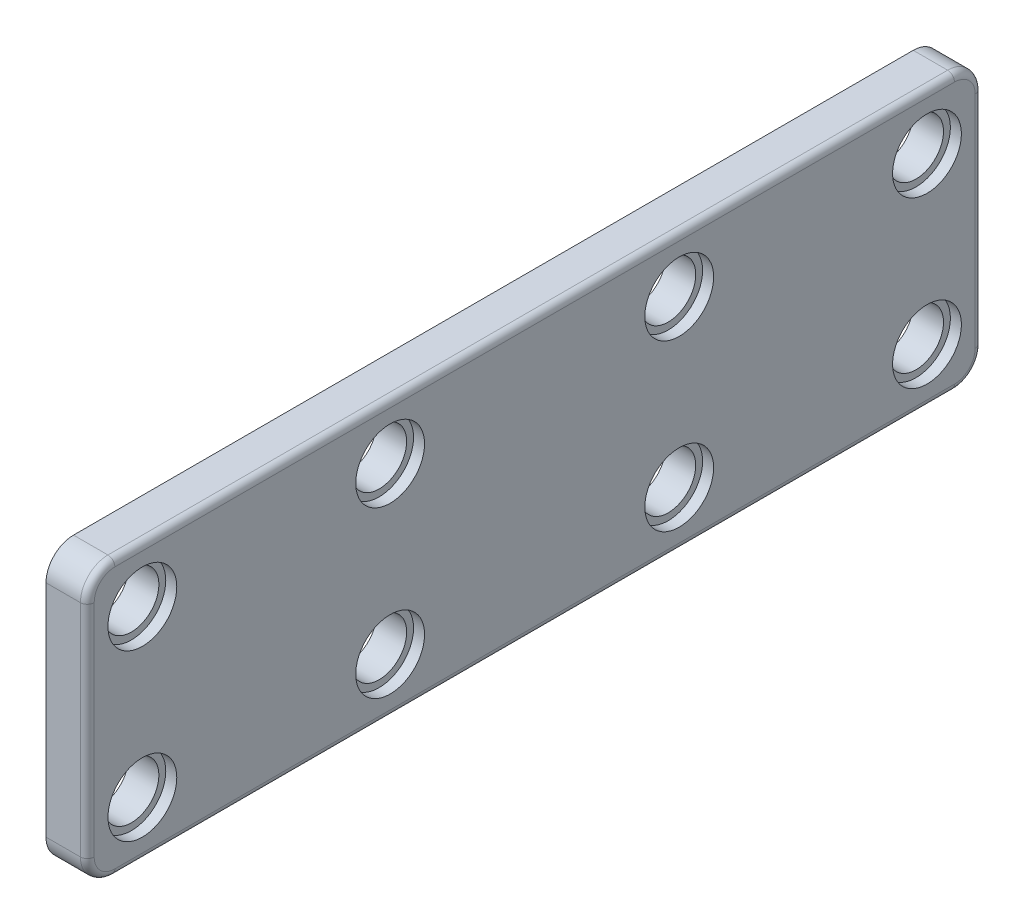
SolidWorks part; units mm, degrees
ref_plane "Front Plane" through (0, 0, 0) normal (0, 0, 1) x (1, 0, 0)
ref_plane "Top Plane" through (0, 0, 0) normal (0, 1, 0) x (1, 0, 0)
ref_plane "Right Plane" through (0, 0, 0) normal (1, 0, 0) x (0, 0, -1)
sketch "Sketch2" plane through (0, 0, 0) normal (0, 0, 1) x (1, 0, 0)
  line L1 (-1.5, -10) -> (1.5, -10)
  line L2 (-1.5, -10) -> (-1.5, 10)
  line L3 (-1.5, 10) -> (1.5, 10)
  line L4 (1.5, -10) -> (1.5, 10)
  line L5 (-1.5, -10) -> (1.5, 10) construction
  line L6 (-1.5, 10) -> (1.5, -10) construction
  point P0 (0, 0)
  dimension "D1" = 20
  dimension "D2" = 3
extrude "Boss-Extrude2" add sketch "Sketch2" along normal blind 65
fillet "Fillet3" radius 2 1 edges at (0, 10, 65)
fillet "Fillet4" radius 2 1 edges at (0, -10, 65)
fillet "Fillet5" radius 2 1 edges at (0, 10, 0)
fillet "Fillet6" radius 2 1 edges at (0, -10, 0)
sketch "Sketch3" plane through (1.5, 0, 0) normal (1, 0, 0) x (0, 0, -1)
  line L0 (-86.0874, 0) -> (15.1847, 0) construction
  line L2 (-65, -8) -> (-65, 8) construction
  line L3 (-32.5, 10) -> (-32.5, -20.1361) construction
  line L4 (-63, 10) -> (-2, 10) construction
  point P3 (-61, 6)
  dimension "D1" = 6
  dimension "D2" = 4
hole_wizard "CBORE for M5 Hex Head Bolt1" positions "Sketch5" profile "Sketch4" counterbore size "M5" standard "DIN"
sketch "Sketch5" plane through (1.5, 0, 0) normal (1, 0, 0) x (0, 0, -1)
  point P0 (-61, 6)
sketch "Sketch4" plane through (1.5, 6, 61) normal (0, 1, 0) x (0, 0, -1)
  line L0 (0, 0) -> (0, 5.1781)
  line L1 (0, 5.1781) -> (2, 4)
  line L2 (2, 4) -> (2, 0.8)
  line L3 (2, 0.8) -> (2.5, 0.8)
  line L4 (2.5, 0.8) -> (2.5, 0)
  line L5 (2.5, 0) -> (0, 0)
  line L10 (0, 5.1781) -> (-2, 4) construction
  line L11 (0, -6.35) -> (0, 107.95) construction
  dimension "Hole Dia." = 4
  dimension "Hole Depth" = 4
  dimension "C'Bore Dia." = 5
  dimension "C'Bore Depth" = 0.8
  dimension "Drill Angle" = 119
pattern_linear "LPattern1" count 2 spacing 18 along (0, 0, -1) count 2 spacing 12 along (0, -1, 0) of "CBORE for M5 Hex Head Bolt1"
ref_plane "Plane1" through (0, 0, 32.5) normal (0, 0, 1) x (0, -1, 0)
mirror "Mirror16" about plane through (0, 0, 32.5) normal (0, 0, 1) of "LPattern1", "CBORE for M5 Hex Head Bolt1"
fillet "Fillet7" radius 0.5 8 edges at (1.5, -9.4142, 64.4142) (1.5, 0, 65) (1.5, 9.4142, 64.4142) (1.5, 10, 32.5) (1.5, 9.4142, 0.5858) (1.5, 0, 0) (1.5, -9.4142, 0.5858) (1.5, -10, 32.5)
